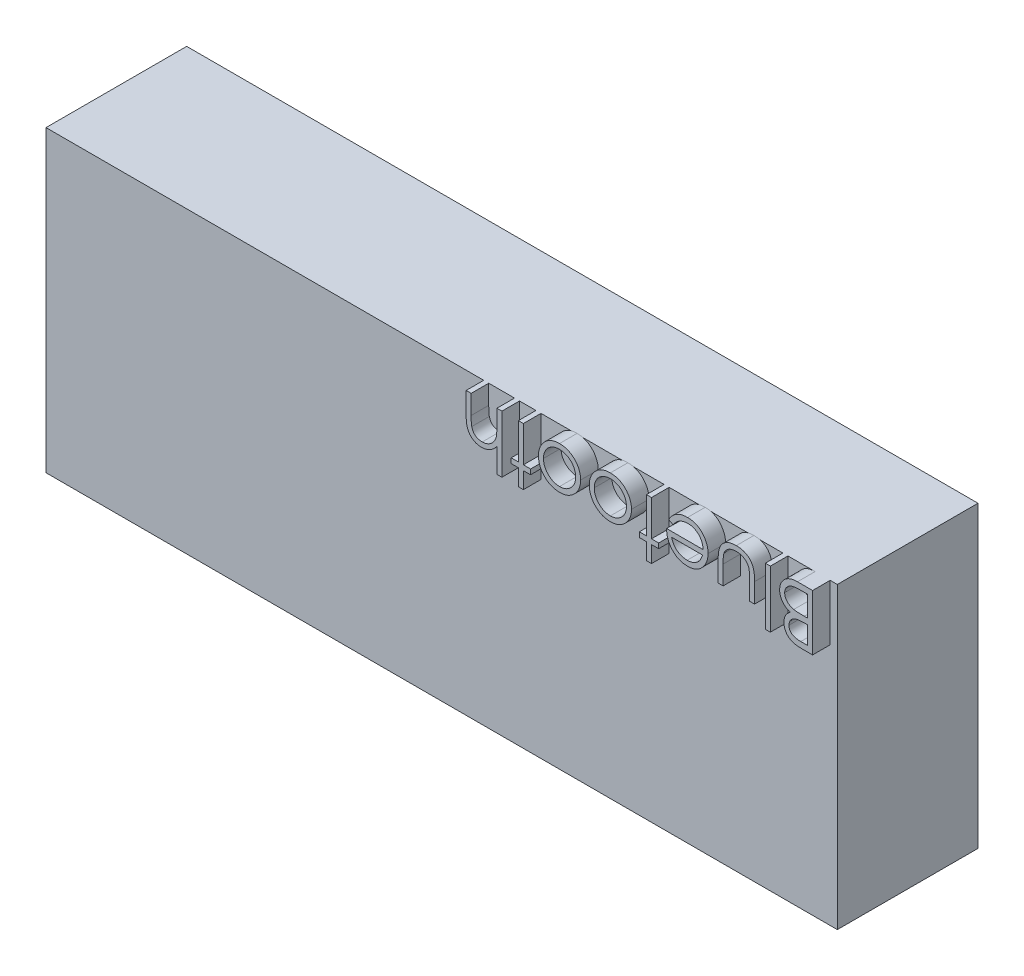
SolidWorks part; units mm, degrees
ref_plane "Front Plane" through (0, 0, 0) normal (0, 0, 1) x (1, 0, 0)
ref_plane "Top Plane" through (0, 0, 0) normal (0, 1, 0) x (1, 0, 0)
ref_plane "Right Plane" through (0, 0, 0) normal (1, 0, 0) x (0, 0, -1)
sketch "Sketch1" plane through (0, 0, 0) normal (0, 0, 1) x (1, 0, 0)
  line L1 (-45, 17) -> (0, 17)
  line L2 (-45, 17) -> (-45, 0)
  line L3 (-45, 0) -> (0, 0)
  line L4 (0, 17) -> (0, 0)
  dimension "D1" = 45
  dimension "D2" = 17
extrude "Boss-Extrude1" add sketch "Sketch1" along normal blind 8
sketch "Sketch2" plane through (0, 0, 8) normal (0, 0, 1) x (1, 0, 0)
  text T0 "Bluetooth\r\n"
extrude "Boss-Extrude2" add sketch "Sketch2" along normal blind 1
